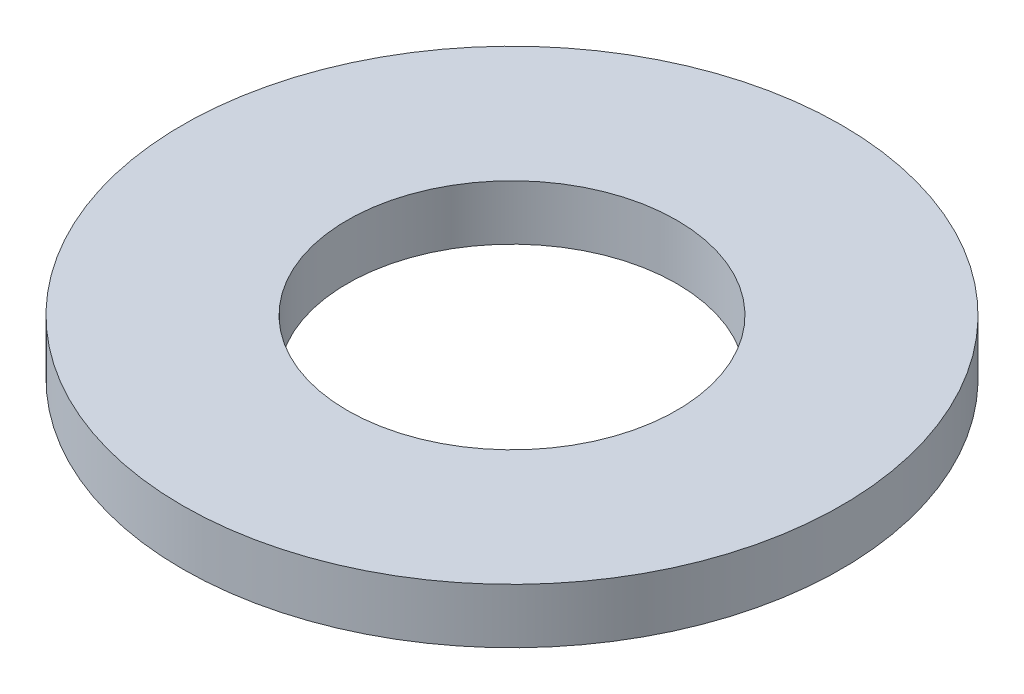
SolidWorks part; units mm, degrees
material "AISI 304"
ref_plane "前视基准面" through (0, 0, 0) normal (0, 0, 1) x (1, 0, 0)
ref_plane "上视基准面" through (0, 0, 0) normal (0, 1, 0) x (1, 0, 0)
ref_plane "右视基准面" through (0, 0, 0) normal (1, 0, 0) x (0, 0, -1)
sketch "草图1" plane through (0, 0, 0) normal (0, 1, 0) x (1, 0, 0)
  circle A0 centre (0, 0) radius 1.5
  circle A1 centre (0, 0) radius 3
  dimension "D1" = 3
  dimension "D2" = 6
extrude "凸台-拉伸1" add sketch "草图1" along normal blind 0.5
